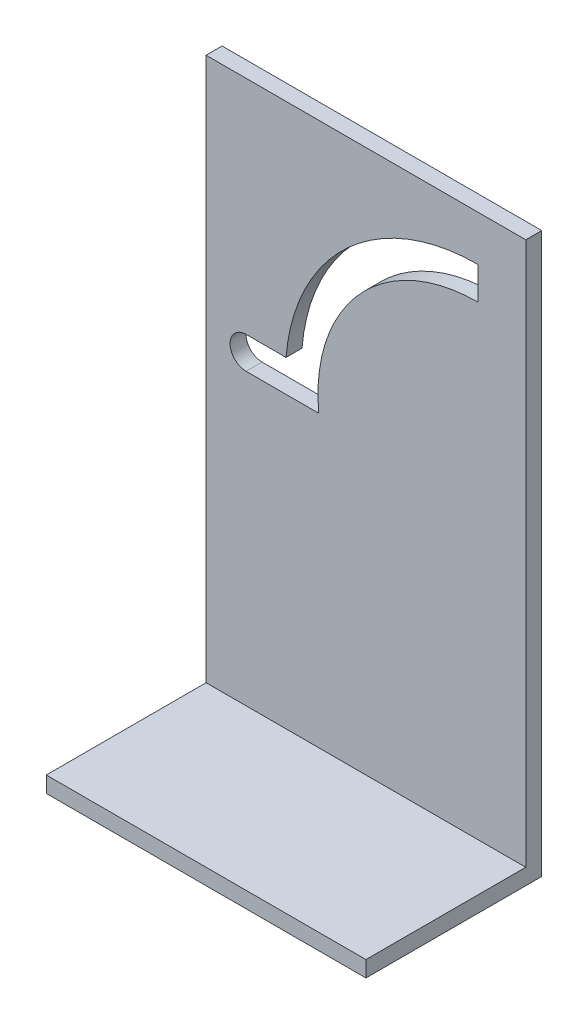
SolidWorks part; units mm, degrees
ref_plane "前视基准面" through (0, 0, 0) normal (0, 0, 1) x (1, 0, 0)
ref_plane "上视基准面" through (0, 0, 0) normal (0, 1, 0) x (1, 0, 0)
ref_plane "右视基准面" through (0, 0, 0) normal (1, 0, 0) x (0, 0, -1)
sketch "草图1" plane through (0, 0, 0) normal (0, 0, 1) x (1, 0, 0)
  line L0 (-30.2714, 30.2806) -> (-30.2714, -39.7194)
  line L1 (-30.2714, -39.7194) -> (9.7286, -39.7194)
  line L2 (9.7286, -39.7194) -> (9.7286, 30.2806)
  line L3 (9.7286, 30.2806) -> (-30.2714, 30.2806)
  line L4 (-30.2714, -39.7194) -> (-25.2714, -39.7194) construction
  line L5 (-25.2714, -39.7194) -> (-25.2714, 0.5306) construction
  line L6 (-25.2714, -1.4694) -> (-20.2714, -1.4694)
  line L7 (-25.2714, 2.5306) -> (-20.2714, 2.5306)
  line L8 (-20.2714, 0.5306) -> (-20.2714, -1.4694) construction
  line L9 (-20.2714, 0.5306) -> (3.7286, 0.5306) construction
  line L10 (-20.2714, -1.4694) -> (-16.1712, -1.4694)
  line L11 (3.7286, 20.5306) -> (3.7286, 24.6138)
  arc A0 (-25.2714, 2.5306) -> (-25.2714, -1.4694) centre (-25.2714, 0.5306) ccw
  arc A1 (3.7286, 24.6138) -> (-20.2714, 2.5306) centre (3.7286, 0.5306) ccw
  arc A2 (3.7286, 20.5306) -> (-16.1712, -1.4694) centre (3.7286, 0.5306) ccw
  dimension "D5" = 4
  dimension "D8" = 40
  dimension "D1" = 70
  dimension "D2" = 40
  dimension "D3" = 5
  dimension "D4" = 40.25
  dimension "D6" = 5
  dimension "D7" = 24
extrude "凸台-拉伸1" add sketch "草图1" along normal blind 2
sketch "草图2" plane through (0, 0, 2) normal (0, 0, 1) x (1, 0, 0)
  line L0 (-30.2714, -39.7194) -> (-30.2714, -37.7194)
  line L1 (-30.2714, 30.2806) -> (-30.2714, -39.7194) construction
  line L2 (-30.2714, -37.7194) -> (9.7286, -37.7194)
  line L3 (9.7286, -39.7194) -> (9.7286, 30.2806) construction
  line L4 (9.7286, -37.7194) -> (9.7286, -39.7194)
  line L5 (9.7286, -39.7194) -> (-30.2714, -39.7194)
  dimension "D1" = 2
extrude "凸台-拉伸2" add sketch "草图2" along normal blind 20
